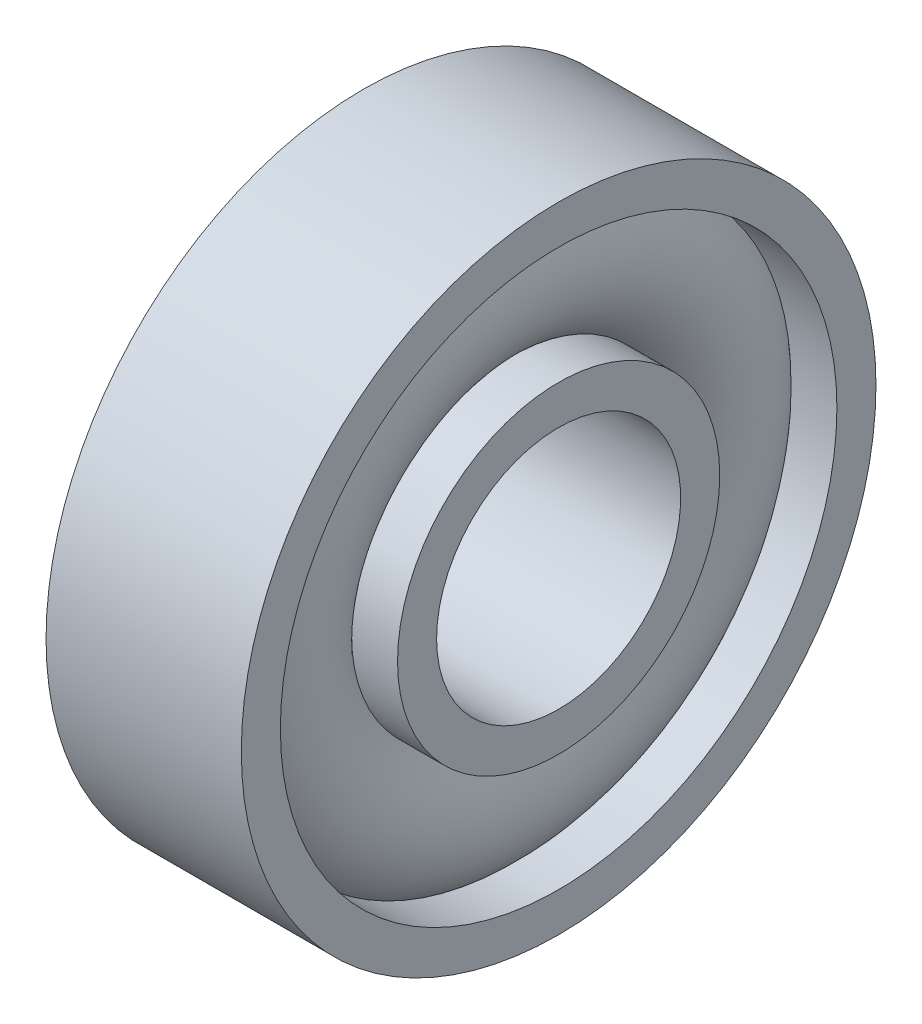
SolidWorks part; units mm, degrees
ref_plane "Plan de face" through (0, 0, 0) normal (0, 0, 1) x (1, 0, 0)
ref_plane "Plan de dessus" through (0, 0, 0) normal (0, 1, 0) x (1, 0, 0)
ref_plane "Plan de droite" through (0, 0, 0) normal (1, 0, 0) x (0, 0, -1)
sketch "Esquisse1" plane through (0, 0, 0) normal (0, 0, 1) x (1, 0, 0)
  line L0 (-3.5015, 0) -> (3.5015, 0) construction
  line L1 (-2, 6.5) -> (2, 6.5)
  line L2 (2, 6.5) -> (2, 5.7)
  line L3 (2, 5.7) -> (1.0583, 5.7)
  line L4 (1.0583, 3.3) -> (2, 3.3)
  line L5 (2, 3.3) -> (2, 2.5)
  line L6 (2, 2.5) -> (-2, 2.5)
  line L7 (0, 0) -> (0, 8.7171) construction
  line L8 (-2, 3.3) -> (-2, 2.5)
  line L9 (-1.0583, 3.3) -> (-2, 3.3)
  line L10 (-2, 5.7) -> (-1.0583, 5.7)
  line L11 (-2, 6.5) -> (-2, 5.7)
  arc A0 (1.0583, 5.7) -> (1.0583, 3.3) centre (0, 4.5) cw
  arc A1 (-1.0583, 5.7) -> (-1.0583, 3.3) centre (0, 4.5) ccw
  point P17 (0, 2.5)
  point P20 (0, 6.5)
  dimension "D3" = 1.6
  dimension "D1" = 13
  dimension "D2" = 5
  dimension "D4" = 0.8
  dimension "D5" = 4
revolve "Révolution1" add sketch "Esquisse1" angle 360 about L0
